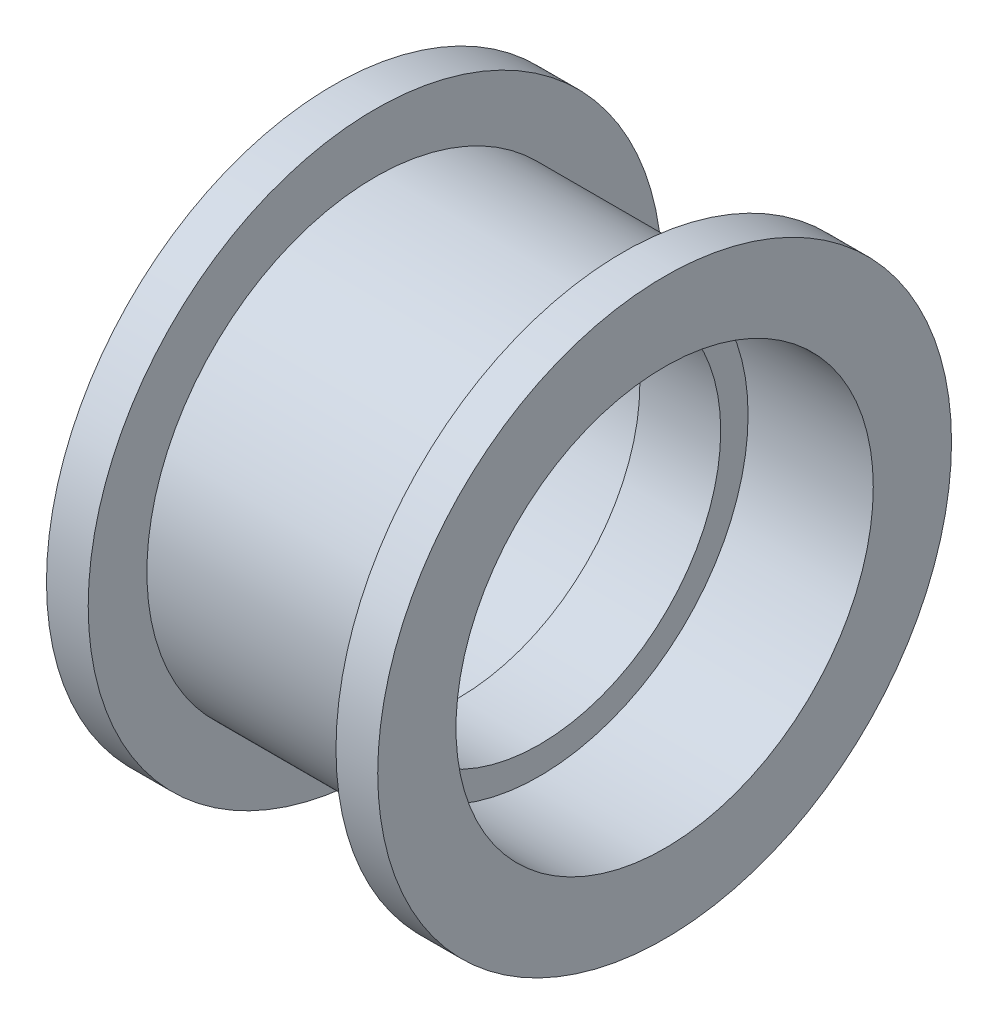
SolidWorks part; units mm, degrees
material "Delrin 2700 NC010, Low Viscosity Acetal Copolymer (SS)"
ref_plane "Front Plane" through (0, 0, 0) normal (0, 0, 1) x (1, 0, 0)
ref_plane "Top Plane" through (0, 0, 0) normal (0, 1, 0) x (1, 0, 0)
ref_plane "Right Plane" through (0, 0, 0) normal (1, 0, 0) x (0, 0, -1)
sketch "Sketch1" plane through (0, 0, 0) normal (0, 0, 1) x (1, 0, 0)
  line L0 (1.55, 6.95) -> (-1.55, 6.95)
  line L1 (-1.55, 6.95) -> (-1.55, 8)
  line L2 (-1.55, 8) -> (-6.35, 8)
  line L3 (-6.35, 8) -> (-6.35, 11)
  line L4 (-6.35, 11) -> (-4.75, 11)
  line L5 (-4.75, 8.75) -> (4.75, 8.75)
  line L6 (0, 8.75) -> (0, 6.95) construction
  line L7 (-4.75, 11) -> (-4.75, 8.75)
  line L8 (6.35, 8) -> (6.35, 11)
  line L9 (1.55, 8) -> (6.35, 8)
  line L10 (1.55, 6.95) -> (1.55, 8)
  line L11 (0, 0) -> (-12.6359, 0) construction
  line L12 (4.75, 11) -> (4.75, 8.75)
  line L13 (6.35, 11) -> (4.75, 11)
  dimension "D1" = 1.6
  dimension "8.64" = 13.9
  dimension "D2" = 16
  dimension "D3" = 17.5
  dimension "D4" = 3.1
  dimension "D5" = 22
  dimension "D6" = 12.7
revolve "Revolve1" add sketch "Sketch1" angle 360 about L11
